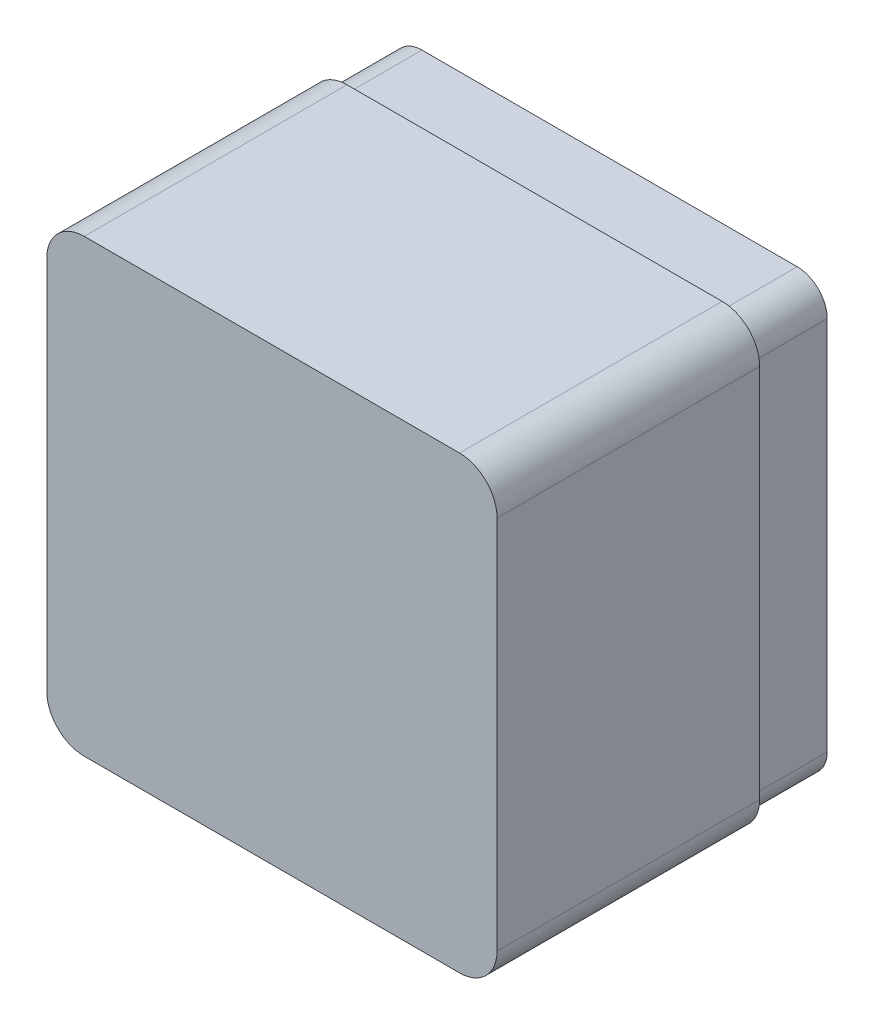
SolidWorks part; units mm, degrees
ref_plane "Front Plane" through (0, 0, 0) normal (0, 0, 1) x (1, 0, 0)
ref_plane "Top Plane" through (0, 0, 0) normal (0, 1, 0) x (1, 0, 0)
ref_plane "Right Plane" through (0, 0, 0) normal (1, 0, 0) x (0, 0, -1)
sketch "Sketch1" plane through (0, 0, 0) normal (0, 0, 1) x (1, 0, 0)
  line L1 (0, 0) -> (120, 0)
  line L2 (0, 0) -> (0, -120)
  line L3 (0, -120) -> (120, -120)
  line L4 (120, 0) -> (120, -120)
  dimension "D1" = 120
  dimension "D2" = 120
extrude "Boss-Extrude1" add sketch "Sketch1" along normal blind 90
fillet "Fillet1" radius 10 4 edges at (120, -120, 45) (0, -120, 45) (0, 0, 45) (120, 0, 45)
shell "Shell1" thickness 4
sketch "Sketch2" plane through (0, 0, 0) normal (0, 0, -1) x (-1, 0, 0)
  line L0 (-118, -10) -> (-118, -110)
  line L1 (-110, -118) -> (-10, -118)
  line L2 (-2, -110) -> (-2, -10)
  line L3 (-10, -2) -> (-110, -2)
  line L4 (-120, -10) -> (-120, -110)
  line L5 (-110, -120) -> (-10, -120)
  line L6 (0, -110) -> (0, -10)
  line L7 (-10, 0) -> (-110, 0)
  line L8 (-120, -10) -> (-120, -110)
  line L9 (-110, -120) -> (-10, -120)
  line L10 (0, -110) -> (0, -10)
  line L11 (-10, 0) -> (-110, 0)
  arc A0 (-118, -110) -> (-110, -118) centre (-110, -110) ccw
  arc A1 (-10, -118) -> (-2, -110) centre (-10, -110) ccw
  arc A2 (-2, -10) -> (-10, -2) centre (-10, -10) ccw
  arc A3 (-110, -2) -> (-118, -10) centre (-110, -10) ccw
  arc A4 (-120, -110) -> (-110, -120) centre (-110, -110) ccw
  arc A5 (-10, -120) -> (0, -110) centre (-10, -110) ccw
  arc A6 (0, -10) -> (-10, 0) centre (-10, -10) ccw
  arc A7 (-110, 0) -> (-120, -10) centre (-110, -10) ccw
  arc A8 (-120, -110) -> (-110, -120) centre (-110, -110) ccw
  arc A9 (-10, -120) -> (0, -110) centre (-10, -110) ccw
  arc A10 (0, -10) -> (-10, 0) centre (-10, -10) ccw
  arc A11 (-110, 0) -> (-120, -10) centre (-110, -10) ccw
  dimension "D1" = 0
  dimension "D2" = 2
extrude "Cut-Extrude1" cut sketch "Sketch2" against normal blind 20
